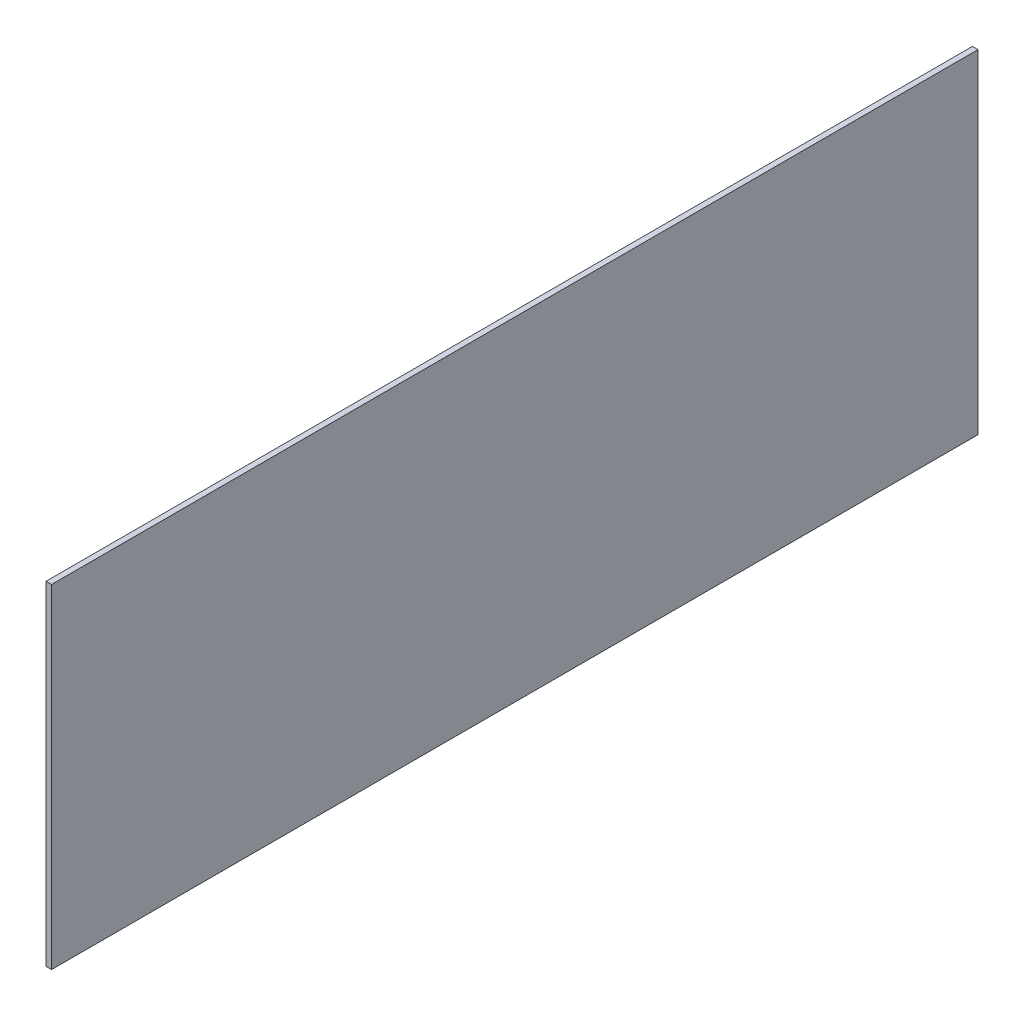
SolidWorks part; units mm, degrees
ref_plane "Спереди" through (0, 0, 0) normal (0, 0, 1) x (1, 0, 0)
ref_plane "Сверху" through (0, 0, 0) normal (0, 1, 0) x (1, 0, 0)
ref_plane "Справа" through (0, 0, 0) normal (1, 0, 0) x (0, 0, -1)
sketch "Эскиз1" plane through (0, 0, 0) normal (1, 0, 0) x (0, 0, -1)
  line L1 (0, 0) -> (5000, 0)
  line L2 (0, 0) -> (0, 1800)
  line L3 (0, 1800) -> (5000, 1800)
  line L4 (5000, 0) -> (5000, 1800)
extrude "Бобышка-Вытянуть1" add sketch "Эскиз1" along normal blind 30
